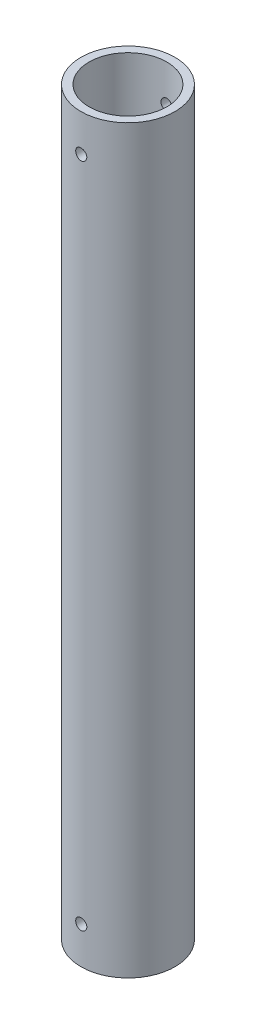
SolidWorks part; units mm, degrees
ref_plane "Alzado" through (0, 0, 0) normal (0, 0, 1) x (1, 0, 0)
ref_plane "Planta" through (0, 0, 0) normal (0, 1, 0) x (1, 0, 0)
ref_plane "Vista lateral" through (0, 0, 0) normal (1, 0, 0) x (0, 0, -1)
sketch "Croquis1" plane through (0, 0, 0) normal (0, 1, 0) x (1, 0, 0)
  circle A0 centre (0, 0) radius 10.5
  circle A1 centre (0, 0) radius 12.7
  dimension "D1" = 25.4
  dimension "D2" = 21
extrude "Saliente-Extruir1" add sketch "Croquis1" along normal blind 200
sketch "Croquis2" plane through (0, 0, 0) normal (0, 0, 1) x (1, 0, 0)
  line L0 (0, 0) -> (0, 10) construction
  line L1 (0, 10) -> (0, 190) construction
  line L2 (0, 190) -> (0, 200) construction
  line L3 (10.5, 200) -> (-10.5, 200) construction
  circle A0 centre (0, 190) radius 1.5
  circle A1 centre (0, 10) radius 1.5
  dimension "D3" = 3
  dimension "D1" = 10
  dimension "D2" = 10
extrude "Cortar-Extruir1" cut sketch "Croquis2" against normal through all and the other way through all
